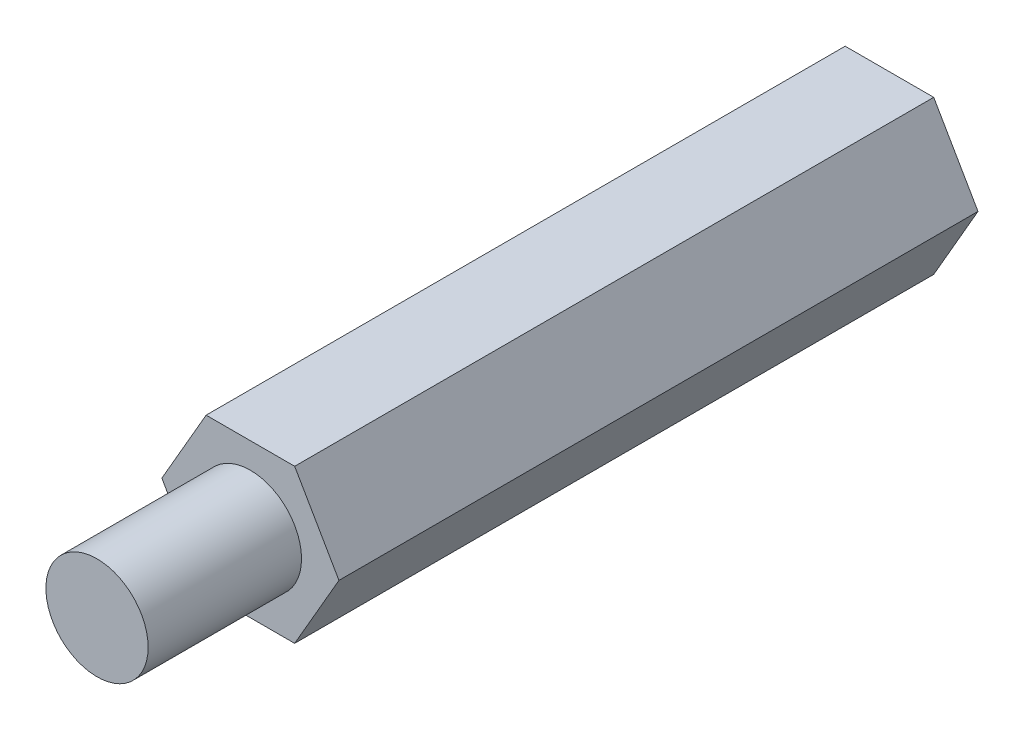
SolidWorks part; units mm, degrees
ref_plane "Front Plane" through (0, 0, 0) normal (0, 0, 1) x (1, 0, 0)
ref_plane "Top Plane" through (0, 0, 0) normal (0, 1, 0) x (1, 0, 0)
ref_plane "Right Plane" through (0, 0, 0) normal (1, 0, 0) x (0, 0, -1)
sketch "Sketch1" plane through (0, 0, 0) normal (0, 0, 1) x (1, 0, 0)
  line L1 (3.4641, 0) -> (1.7321, 3)
  line L2 (1.7321, 3) -> (-1.7321, 3)
  line L3 (-1.7321, 3) -> (-3.4641, 0)
  line L4 (-3.4641, 0) -> (-1.7321, -3)
  line L5 (-1.7321, -3) -> (1.7321, -3)
  line L6 (1.7321, -3) -> (3.4641, 0)
  circle A0 centre (0, 0) radius 3 construction
  dimension "D1" = 6
extrude "Boss-Extrude1" add sketch "Sketch1" along normal blind 25
sketch "Sketch2" plane through (0, 0, 25) normal (0, 0, 1) x (1, 0, 0)
  circle A0 centre (0, 0) radius 2
  dimension "D1" = 4
extrude "Boss-Extrude2" add sketch "Sketch2" along normal blind 6
hole_wizard "M4x0.7 Tapped Hole1" positions "Sketch3" profile "Sketch4" tap size "M4x0.7" standard "ANSI Metric"
sketch "Sketch3" plane through (0, 0, 0) normal (0, 0, -1) x (-1, 0, 0)
  point P0 (0, 0)
sketch "Sketch4" plane through (0, 0, 0) normal (1, 0, 0) x (0, 1, 0)
  line L0 (0, 0) -> (0, 11.0914)
  line L1 (0, 11.0914) -> (1.65, 10.1)
  line L2 (1.65, 10.1) -> (1.65, 0)
  line L5 (1.65, 0) -> (0, 0)
  line L10 (0, 11.0914) -> (-1.65, 10.1) construction
  line L11 (0, -6.35) -> (0, 107.95) construction
  dimension "Tap Drill Dia." = 3.3
  dimension "Tap Drill Depth" = 10.1
  dimension "Drill Angle" = 118
